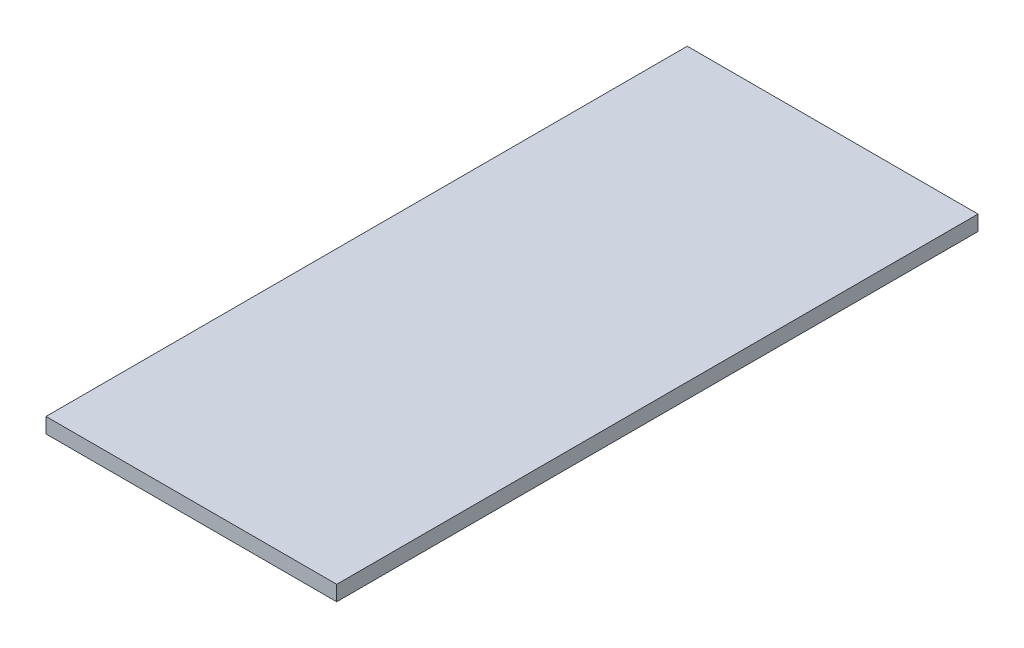
SolidWorks part; units mm, degrees
ref_plane "Спереди" through (0, 0, 0) normal (0, 0, 1) x (1, 0, 0)
ref_plane "Сверху" through (0, 0, 0) normal (0, 1, 0) x (1, 0, 0)
ref_plane "Справа" through (0, 0, 0) normal (1, 0, 0) x (0, 0, -1)
sketch "Эскиз1" plane through (0, 0, 0) normal (0, 1, 0) x (1, 0, 0)
  line L1 (172.5, -380.5) -> (-172.5, -380.5)
  line L2 (172.5, -380.5) -> (172.5, 380.5)
  line L3 (172.5, 380.5) -> (-172.5, 380.5)
  line L4 (-172.5, -380.5) -> (-172.5, 380.5)
  line L5 (172.5, -380.5) -> (-172.5, 380.5) construction
  line L6 (172.5, 380.5) -> (-172.5, -380.5) construction
  point P0 (0, 0)
  dimension "D1" = 345
  dimension "D2" = 761
extrude "Бобышка-Вытянуть1" add sketch "Эскиз1" along normal blind 18
